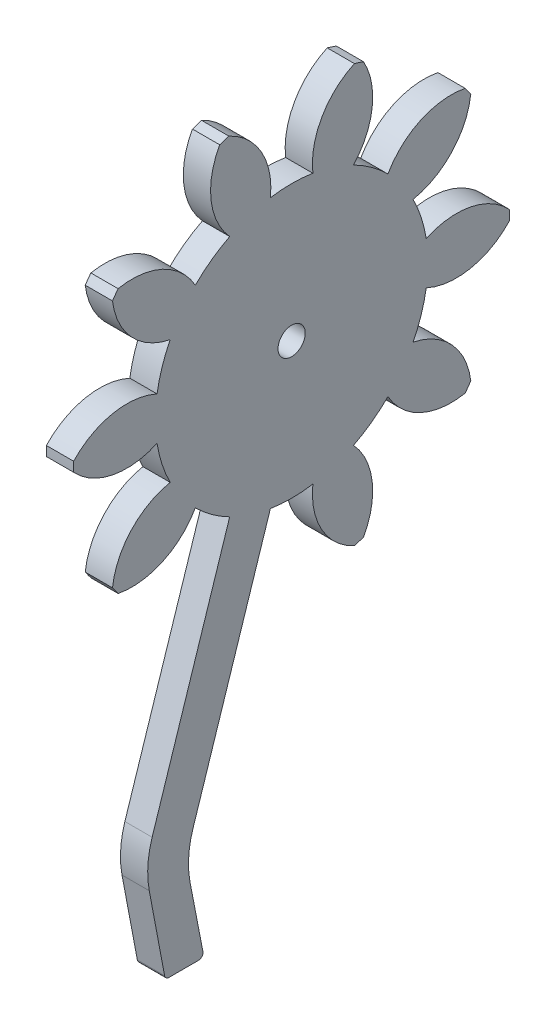
SolidWorks part; units mm, degrees
ref_plane "Plane1" through (0, 0, 0) normal (0, 0, 1) x (1, 0, 0)
ref_plane "Plane2" through (0, 0, 0) normal (0, 1, 0) x (1, 0, 0)
ref_plane "Plane3" through (0, 0, 0) normal (1, 0, 0) x (0, 0, -1)
sketch "HoldingSke" plane through (0, 0, 0) normal (0, 1, 0) x (1, 0, 0)
  line L0 (0, 0) -> (0.2462, -0.0434)
  line L1 (-15, 0) -> (100, 0) construction
  line L2 (0, 0) -> (-2.1039, 2.3779)
  line L3 (0, 0) -> (-11.863, 4.5341)
  line L4 (0, 0) -> (8.5048, 1.4996)
  line L5 (0, 0) -> (-46.8476, -17.4728)
  line L6 (0, 0) -> (-2.4869, -1.6779)
  line L7 (-2.1039, 2.3779) -> (8.6586, 51.2059)
  line L8 (-76.2, 54.61) -> (-75.7, 54.61)
  line L9 (-71.009, 38.7566) -> (-53.1078, 45.2721)
  line L10 (-76.2, 71.12) -> (104.1128, 71.12)
  line L11 (0, 0) -> (-3, 0)
  line L12 (-76.2, 101.6) -> (-76.073, 101.6)
  line L13 (24.9733, 27.94) -> (52.9518, 28.4284)
  line L14 (24.9733, 27.94) -> (24.9743, 27.94)
  line L15 (24.9733, 27.94) -> (100.4006, 29.5858)
  line L16 (-63.627, -4) -> (-12.827, -4)
  circle A0 centre (0, 0) radius 1.5
  circle A1 centre (0, 0) radius 14.999
  circle A2 centre (0, 0) radius 37.5
  circle A3 centre (0, 0) radius 1.5
  dimension "MHD" = 29.998
  dimension "Hub_dia" = 75
  dimension "Bore" = 3
  dimension "MBD" = 3
  dimension "Num_teeth" = 10
  dimension "Pitch" = 0.25
  dimension "Overall_len" = 50
  dimension "Show_teeth" = 10
  dimension "Thickness" = 3
  dimension "OAL" = 50.0001
  dimension "T_dim" = 0.5
  dimension "Ap" = 20
  dimension "H" = 19.05
  dimension "Pitch_radius" = 180.3128
  dimension "Width" = 3
  dimension "Backlash" = 0.127
  dimension "Addendum_fac" = 1
  dimension "Dedendum_fac" = 1.25
  dimension "Clearance_fac" = 0.25
  dimension "Dedendum_add" = 0.001
  dimension "Module" = 4
sketch "BasProSke" plane through (0, 0, 0) normal (0, 1, 0) x (1, 0, 0)
  line L0 (-10, 0) -> (60, 0) construction
  line L1 (0, 0) -> (0, 24)
  line L2 (0, 0) -> (3, 0)
  line L3 (3, 0) -> (3, 24)
  line L4 (3, 24) -> (0, 24)
  dimension "Thickness" = 3
  dimension "Diameter" = 48
revolve "Base-Revolve" add sketch "BasProSke" angle 360 about L0
sketch "TooCutSke" plane through (0, 0, 0) normal (1, 0, 0) x (0, 0, -1)
  line L1 (0, 0) -> (0, 107) construction
  line L2 (0, 0) -> (-3.3505, 19.7173) construction
  line L3 (0, 0) -> (-12.2295, 37.6384) construction
  line L4 (-3.3505, 19.7173) -> (-6.1147, 18.8192) construction
  arc A0 (2.338, 14.8157) -> (-2.338, 14.8157) centre (0, 0) ccw
  arc A1 (6.9466, 22.9992) -> (-6.9466, 22.9992) centre (0, 0) ccw
  circle A2 centre (0, 0) radius 20 construction
  circle A3 centre (0, 0) radius 18.7939 construction
  arc A4 (-2.338, 14.8157) -> (-6.9466, 22.9992) centre (-10.2857, 15.7294) ccw
  arc A5 (6.9466, 22.9992) -> (2.338, 14.8157) centre (10.2857, 15.7294) ccw
  dimension "Root_dia" = 29.998
  dimension "Overcut_dia" = 48.0508
  dimension "Pitch_dia" = 40
  dimension "Base_dia" = 37.5877
  dimension "Flank_rad" = 8
  dimension "Half_ang" = 18
  dimension "Half_CT" = 2.9064
extrude "ToothCut" cut sketch "TooCutSke" along normal through all
fillet "Breaks" [suppressed] radius 0.08
fillet "RootFillets" [suppressed] radius 1.001
pattern_circular "TeethCuts" count 10 every 36 about axis through (-10, 0, 0) along (1, 0, 0) of "ToothCut", "RootFillets", "Breaks"
sketch "HubNeaOneSke" plane through (0, 0, 0) normal (-1, 0, 0) x (0, 0, 1)
  circle A0 centre (0, 0) radius 14.999
  dimension "Diameter" = 29.998
extrude "HubNearOne" [suppressed] add sketch "HubNeaOneSke" along normal blind 47.0001
sketch "HubNeaBotSke" plane through (0, 0, 0) normal (-1, 0, 0) x (0, 0, 1)
  circle A0 centre (0, 0) radius 14.999
  dimension "Diameter" = 29.998
extrude "HubNearBoth" [suppressed] add sketch "HubNeaBotSke" along normal blind 23.5
ref_plane "FarPln" through (3, 0, 0) normal (1, 0, 0) x (0, 0, -1)
sketch "HubFarSke" plane through (3, 0, 0) normal (1, 0, 0) x (0, 0, -1)
  circle A0 centre (0, 0) radius 14.999
  dimension "Diameter" = 29.998
extrude "HubFar" [suppressed] add sketch "HubFarSke" along normal blind 23.5
sketch "BorSke" plane through (0, 0, 0) normal (1, 0, 0) x (0, 0, -1)
  circle A0 centre (0, 0) radius 1.5
  dimension "Diameter" = 3
extrude "Bore" cut sketch "BorSke" along normal mid plane 100.0001
sketch "KeySke" plane through (0, 0, 0) normal (1, 0, 0) x (0, 0, -1)
  line L0 (-0.6, 0) -> (-0.6, 2)
  line L1 (-0.6, 2) -> (0.6, 2)
  line L2 (0.6, 2) -> (0.6, 0)
  line L3 (0, 0) -> (0, 34) construction
  line L4 (-0.6, 0) -> (0.6, 0)
  dimension "Offset" = 2
  dimension "Width" = 1.2
extrude "Keyway" [suppressed] cut sketch "KeySke" along normal mid plane 100.0001
pattern_circular "Keyway2" [suppressed] count 2 every 90 about axis through (-10, 0, 0) along (1, 0, 0)
sketch "Sketch1" plane through (0, 0, 0) normal (-1, 0, 0) x (0, 0, 1)
  line L0 (6.8169, -13.3604) -> (2.338, -14.8157)
  line L1 (2.338, -14.8157) -> (0, -15.5753)
  line L2 (0, -15.5753) -> (3.8464, -27.4134)
  line L3 (3.8464, -27.4134) -> (12.6035, -24.5681)
  line L4 (12.6035, -24.5681) -> (8.757, -12.73)
  line L5 (8.757, -12.73) -> (6.8169, -13.3604)
  arc A0 (-2.338, -14.8157) -> (2.338, -14.8157) centre (0, 0) ccw construction
  circle A1 centre (0, 0) radius 1.5 construction
  dimension "D1" = 9.2077
  dimension "D2" = 27.2603
  dimension "D3" = 4.3946
extrude "Cut-Extrude1" cut sketch "Sketch1" against normal blind 10
sketch "Sketch2" plane through (0, 0, 0) normal (-1, 0, 0) x (0, 0, 1)
  line L0 (6.8169, -13.3604) -> (2.338, -14.8157)
  line L1 (2.338, -14.8157) -> (11.6663, -43.5252)
  line L2 (11.6663, -43.5252) -> (16.1452, -42.0699)
  line L3 (16.1452, -42.0699) -> (6.8169, -13.3604)
  line L4 (11.6663, -43.5252) -> (9.6486, -53.9291)
  line L5 (16.1452, -42.0699) -> (13.9058, -53.9291)
  line L6 (13.9058, -53.9291) -> (9.6486, -53.9291)
  line L7 (16.1452, -42.0699) -> (11.6663, -43.5252)
  circle A0 centre (0, 0) radius 1.5 construction
  line M7 (2.338, -14.8157) -> (6.8169, -13.3604)
  dimension "D1" = 45
  dimension "D2" = 4.2572
  dimension "D3" = 10.4039
extrude "Boss-Extrude1" add sketch "Sketch2" against normal blind 3 contours L2 L3 L1 M7 | L6 L5 L2 L4
fillet "Fillet1" radius 10 2 edges at (1.5, -42.0699, 16.1452) (1.5, -43.5252, 11.6663)
fillet "Fillet2" radius 0.5 2 edges at (1.5, -53.9291, 13.9058) (1.5, -53.9291, 9.6486)
equation "' \"Module@HoldingSke\" = 6.35"
equation "' \"Num_teeth@HoldingSke\" = 12"
equation "' \"Ap@HoldingSke\" =  20"
equation "' \"Ap@HoldingSke\" = 20"
equation "' \"Width@HoldingSke\" = 0.5 * 25.4"
equation "' \"Hub_dia@HoldingSke\"= 1 * 25.4"
equation "' \"Hub_dia@HoldingSke\" = 1 * 25.4"
equation "' \"Overall_len@HoldingSke\" = 1.0 * 25.4"
equation "' \"Bore@HoldingSke\" = 0.75 * 25.4"
equation "' \"T_dim@HoldingSke\" = 0.1 * 25.4"
equation "' \"Width@KeySke\" = 0.25 * 25.4"
equation "' \"Show_teeth@HoldingSke\" = 13"
equation "' \"Backlash@HoldingSke\" = 0.009 * 25.4"
equation "' \"Addendum_fac@HoldingSke\" = 1.0"
equation "' \"Dedendum_fac@HoldingSke\" = 1.25"
equation "' \"Dedendum_add@HoldingSke\" = 0.00005 * 25.4"
equation "' \"Clearance_fac@HoldingSke\" = 0.25"
equation "\"Pitch@HoldingSke\" = 1 / \"Module@HoldingSke\""
equation "\"Overcut_dia@TooCutSke\" = (\"Num_teeth@HoldingSke\" + 2 * \"Addendum_fac@HoldingSke\") / \"Pitch@HoldingSke\" + 0.002 * 25.4"
equation "\"Pitch_dia@TooCutSke\" = \"Num_teeth@HoldingSke\" / \"Pitch@HoldingSke\""
equation "\"Base_dia@TooCutSke\" = \"Num_teeth@HoldingSke\" / \"Pitch@HoldingSke\" * cos((\"Ap@HoldingSke\"  * 3.14159265 / 180))"
equation "\"Root_dia@TooCutSke\" = (\"Num_teeth@HoldingSke\" + 2) / \"Pitch@HoldingSke\" - 2 * (\"Addendum_fac@HoldingSke\" + \"Dedendum_fac@HoldingSke\") / \"Pitch@HoldingSke\" - \"Dedendum_add@HoldingSke\" * 2"
equation "\"Half_ang@TooCutSke\" = 180 / \"Num_teeth@HoldingSke\""
equation "\"Half_CT@TooCutSke\" = \"Num_teeth@HoldingSke\" / \"Pitch@HoldingSke\" * sin((3.14159265 / 2 / \"Num_teeth@HoldingSke\")) / 2 - 7 * \"Backlash@HoldingSke\" / 4"
equation "\"Flank_rad@TooCutSke\" = \"Num_teeth@HoldingSke\" / \"Pitch@HoldingSke\" / 5"
equation "\"Radius@RootFillets\" = \"Clearance_fac@HoldingSke\" / \"Pitch@HoldingSke\" + \"Dedendum_add@HoldingSke\""
equation "\"Break_rad@Breaks\" = 0.02 / \"Pitch@HoldingSke\""
equation "\"Thickness@HoldingSke\" = \"Width@HoldingSke\""
equation "\"OAL@HoldingSke\" = \"Thickness@HoldingSke\""
equation "\"MHD@HoldingSke\" = (\"Num_teeth@HoldingSke\" + 2) / \"Pitch@HoldingSke\" - 2 * (\"Addendum_fac@HoldingSke\" + \"Dedendum_fac@HoldingSke\")  / \"Pitch@HoldingSke\" - \"Dedendum_add@HoldingSke\" * 2"
equation "\"MBD@HoldingSke\" = (\"Num_teeth@HoldingSke\" + 2) / \"Pitch@HoldingSke\" - 2 * (\"Addendum_fac@HoldingSke\" + \"Dedendum_fac@HoldingSke\")  / \"Pitch@HoldingSke\" - \"Dedendum_add@HoldingSke\" * 2 - 0.002 * 25.4"
equation "\"MHD@HoldingSke\" = ((sgn( \"MHD@HoldingSke\" - \"Hub_dia@HoldingSke\" )-1)*( \"MHD@HoldingSke\" - \"Hub_dia@HoldingSke\" ))/-2+ \"Hub_dia@HoldingSke\""
equation "\"MBD@HoldingSke\" = ((sgn( \"MBD@HoldingSke\" - \"Bore@HoldingSke\" )-1)*( \"MBD@HoldingSke\" - \"Bore@HoldingSke\" ))/-2+ \"Bore@HoldingSke\""
equation "\"OAL@HoldingSke\" = ((sgn( \"OAL@HoldingSke\" - \"Overall_len@HoldingSke\" )+1)*( \"OAL@HoldingSke\" - \"Overall_len@HoldingSke\" ))/2 + \"Overall_len@HoldingSke\" + 0.000002 * 25.4"
equation "\"Num_teeth@TeethCuts\" = int( \"Show_teeth@HoldingSke\" ) + 1"
equation "\"Num_teeth@TeethCuts\" = ((sgn( \"Num_teeth@TeethCuts\" - \"Num_teeth@HoldingSke\" )-1)*( \"Num_teeth@TeethCuts\" - \"Num_teeth@HoldingSke\" ))/-2+ \"Num_teeth@HoldingSke\""
equation "\"Num_teeth@TeethCuts\" = ((sgn( \"Num_teeth@TeethCuts\" - 2.0)+1)*( \"Num_teeth@TeethCuts\" - 2.0))/2 +2.0"
equation "\"Angle@TeethCuts\" = 360.0 / \"Num_teeth@HoldingSke\""
equation "\"Diameter@BasProSke\" = (\"Num_teeth@HoldingSke\" + 2 * \"Addendum_fac@HoldingSke\") / \"Pitch@HoldingSke\""
equation "\"Thickness@BasProSke\"  = \"Thickness@HoldingSke\""
equation "' \"Fillet_rad@BasProSke\" =  \"Thickness@HoldingSke\" * 0.05"
equation "' \"Fillet_rad@BasProSke\" = \"Thickness@HoldingSke\" * 0.05"
equation "\"MHD@HoldingSke\" = ((sgn( \"MHD@HoldingSke\" - \"Root_dia@TooCutSke\" )-1)*( \"MHD@HoldingSke\" - \"Root_dia@TooCutSke\" ))/-2+ \"Root_dia@TooCutSke\""
equation "\"Diameter@HubNeaOneSke\" = \"MHD@HoldingSke\""
equation "\"Length@HubNearOne\" = \"OAL@HoldingSke\" - \"Thickness@BasProSke\""
equation "\"Diameter@HubNeaBotSke\" = \"MHD@HoldingSke\""
equation "\"Length@HubNearBoth\" = ( \"OAL@HoldingSke\" - \"Thickness@BasProSke\" ) / 2.0"
equation "\"Thickness@FarPln\" = \"Thickness@BasProSke\""
equation "\"Diameter@HubFarSke\" = \"MHD@HoldingSke\""
equation "\"Length@HubFar\" = ( \"OAL@HoldingSke\" - \"Thickness@BasProSke\" ) / 2.0"
equation "\"Diameter@BorSke\" = \"MBD@HoldingSke\""
equation "\"D1@Bore\" = \"OAL@HoldingSke\" * 2.0"
equation "\"D1@Keyway\" = \"OAL@HoldingSke\" * 2.0"
equation "\"Offset@KeySke\" = \"T_dim@HoldingSke\" + \"MBD@HoldingSke\" / 2.0"
